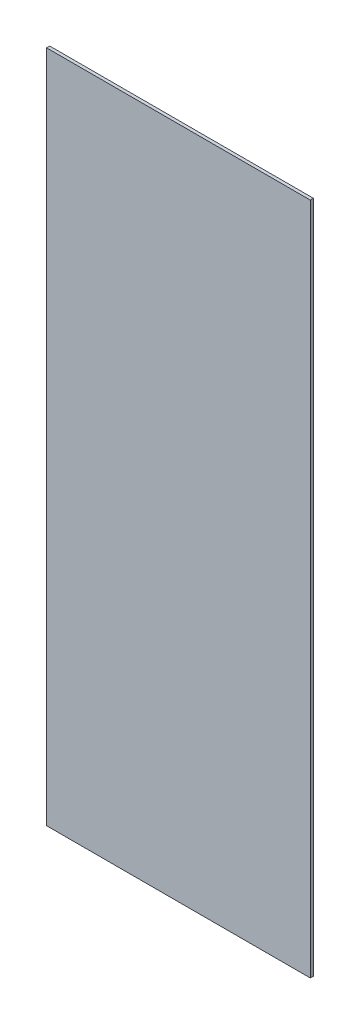
SolidWorks part; units mm, degrees
ref_plane "Přední rovina" through (0, 0, 0) normal (0, 0, 1) x (1, 0, 0)
ref_plane "Horní rovina" through (0, 0, 0) normal (0, 1, 0) x (1, 0, 0)
ref_plane "Pravá rovina" through (0, 0, 0) normal (1, 0, 0) x (0, 0, -1)
sketch "Skica1" plane through (0, 0, 0) normal (0, 0, 1) x (1, 0, 0)
  line L1 (-126.25, 322.5) -> (126.25, 322.5)
  line L2 (-126.25, 322.5) -> (-126.25, -322.5)
  line L3 (-126.25, -322.5) -> (126.25, -322.5)
  line L4 (126.25, 322.5) -> (126.25, -322.5)
  line L5 (-126.25, 322.5) -> (126.25, -322.5) construction
  line L6 (-126.25, -322.5) -> (126.25, 322.5) construction
  point P0 (0, 0)
  dimension "D1" = 252.5
  dimension "D2" = 645
extrude "Přidat vysunutím1" add sketch "Skica1" along normal blind 3
